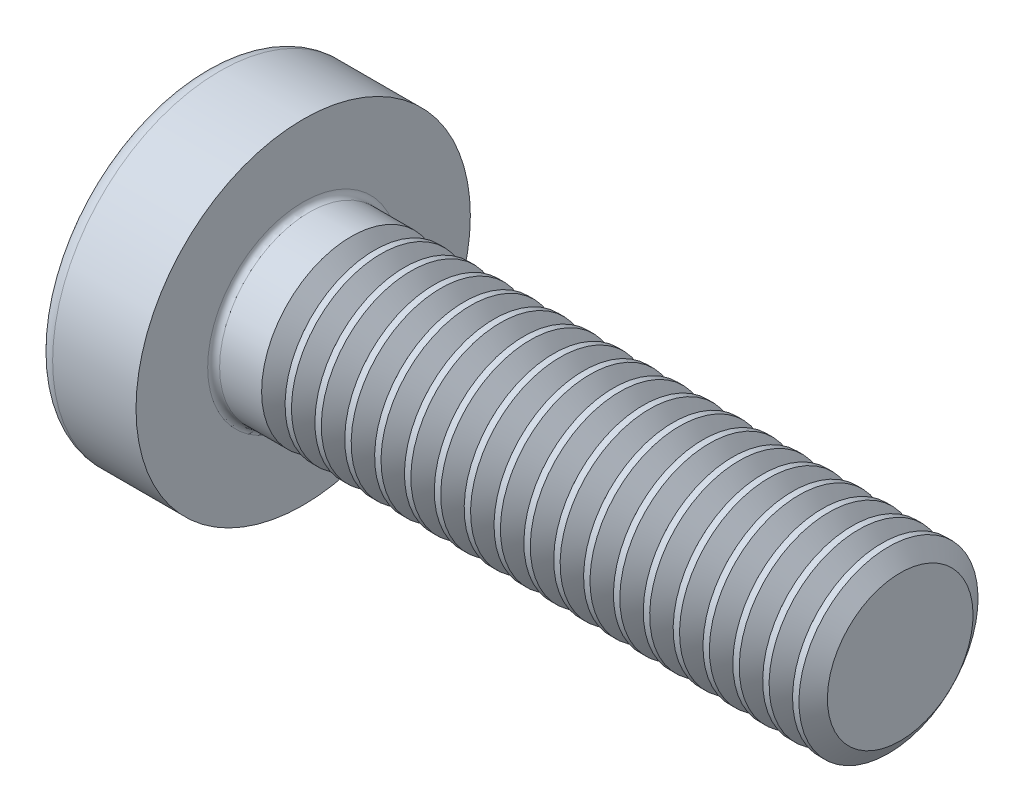
SolidWorks part; units mm, degrees
ref_plane "Plane1" through (0, 0, 0) normal (0, 0, 1) x (1, 0, 0)
ref_plane "Plane2" through (0, 0, 0) normal (0, 1, 0) x (1, 0, 0)
ref_plane "Plane3" through (0, 0, 0) normal (1, 0, 0) x (0, 0, -1)
sketch "BodySke" plane through (0, 0, 0) normal (0, 0, 1) x (1, 0, 0)
  line L0 (2.4, 1.5) -> (2.4, 2.8)
  line L1 (2.65, 6.35) -> (2.65, -3.175) construction
  line L2 (-25.4, 0) -> (127, 0) construction
  line L3 (12.4, 0) -> (0, 0)
  line L4 (2.4, 1.5) -> (12.4, 1.5)
  line L5 (12.4, 1.5) -> (12.4, 0)
  line L6 (1.0035, 2.8) -> (2.4, 2.8)
  line L8 (2.4, 6.35) -> (2.4, -3.175) construction
  arc A0 (0.7754, 2.6744) -> (0, 0) centre (5, 0) ccw
  arc A2 (0.7754, 2.6744) -> (1.0035, 2.8) centre (1.0035, 2.53) cw
  dimension "Head_fillet_rad" = 0.27
  dimension "Head_crown_rad" = 5
  dimension "Head_ht" = 2.4
  dimension "Diameter" = 3
  dimension "Length" = 10
  dimension "Head_dia" = 5.6
  dimension "Advance" = 0.5
  dimension "Thread_nom" = 10
revolve "Base-Revolve" add sketch "BodySke"
cosmetic thread "ThreadCosmetic" [suppressed]
fillet "Fillet1" radius 0.1 1 edges at (2.4, 0, 1.5)
sketch "Sketch3" plane through (0, 0, 0) normal (1, 0, 0) x (0, 0, -1)
  line L0 (0.37, -1.4) -> (-0.37, -1.4)
  line L1 (0.37, -1.4) -> (0.37, 1.4)
  line L2 (-0.37, 1.4) -> (0.37, 1.4)
  line L3 (-0.37, 1.4) -> (-0.37, -1.4)
  dimension "D1" = 1.4
  dimension "Cross_dia" = 2.8
  dimension "D2" = 0.37
  dimension "Cross_width" = 0.74
ref_plane "Plane4" through (1.75, 0, 0) normal (1, 0, 0) x (0, 0, -1)
sketch "Sketch4" plane through (1.75, 0, 0) normal (1, 0, 0) x (0, 0, -1)
  line L0 (0.37, -0.5275) -> (-0.37, -0.5275)
  line L1 (0.37, -0.5275) -> (0.37, 0.5275)
  line L2 (-0.37, 0.5275) -> (0.37, 0.5275)
  line L3 (-0.37, 0.5275) -> (-0.37, -0.5275)
  dimension "D1" = 0.74
  dimension "D2" = 1.055
  dimension "D3" = 0.37
  dimension "D4" = 0.5275
loft "Recess" cut profiles "Sketch3", "Sketch4"
pattern_circular "RecPat" count 2 every 90 about axis through (0, 0, 0) along (1, 0, 0) of "Recess"
sketch "RecCorSke" plane through (0, 0, 0) normal (0, 0, 1) x (1, 0, 0)
  line L0 (-3.175, 0) -> (15.875, 0) construction
  line L1 (-25.4, 0) -> (127, 0) construction
  line L2 (0, 0) -> (0, 0.6784)
  line L3 (0, 0.6784) -> (1.75, 0.556)
  line L4 (1.75, 0.556) -> (1.9307, 0)
  line L5 (1.9307, 0) -> (0, 0)
  dimension "Diameter" = 1.112
  dimension "Depth" = 1.75
  dimension "Draft_angle" = 4
  dimension "Bottom_angle" = 18
revolve "RecessCore" cut sketch "RecCorSke" angle 360 about L0
sketch "ThdSchSke" plane through (0, 0, 0) normal (0, 0, 1) x (1, 0, 0)
  line L0 (3.4, -1.2195) -> (3.2036, -1.5)
  line L1 (3.4, -1.2195) -> (3.5964, -1.5)
  line L2 (3.5964, -1.5) -> (3.5964, -1.875)
  line L3 (-3.175, 0) -> (5.1513, 0) construction
  line L5 (3.5964, -1.875) -> (3.2036, -1.875)
  line L6 (3.2036, -1.875) -> (3.2036, -1.5)
  dimension "Thread_minor" = 2.439
  dimension "Diameter" = 3
  dimension "Start" = 3.4
  dimension "SideAngle" = 55
  dimension "VeeAngle" = 70
  dimension "Overcut" = 3.75
revolve "ThreadSchematic" cut sketch "ThdSchSke" angle 360 about L3
pattern_linear "ThdSchPat" count 19 spacing 0.5 along (1, 0, 0) of "ThreadSchematic"
equation "\"D1@Sketch3\" = \"Cross_dia@Sketch3\" / 2"
equation "\"D2@Sketch3\" = \"Cross_width@Sketch3\" / 2"
equation "\"Depth@RecCorSke\" = \"Cross_depth@Plane4\""
equation "\"D1@Sketch4\" = \"Cross_width@Sketch3\""
equation "\"D2@Sketch4\" = \"Cross_dia@Sketch3\" - 2.0 * \"Cross_depth@Plane4\" * tan(26.5  * 0.017453292)"
equation "\"D3@Sketch4\" = \"D1@Sketch4\" / 2"
equation "\"D4@Sketch4\" = \"D2@Sketch4\" / 2"
equation "\"Thread_length@ThreadCosmetic\" = ((sgn( (\"Length@BodySke\" - \"Advance@BodySke\" * 2.0 ) - \"Thread_nom@BodySke\" )-1)*( (\"Length@BodySke\" - \"Advance@BodySke\" * 2.0 ) - \"Thread_nom@BodySke\" ))/-2+ \"Thread_nom@BodySke\""
equation "\"Thread_minor@ThdSchSke\" = \"Thread_minor@ThreadCosmetic\""
equation "\"Diameter@ThdSchSke\" = \"Diameter@BodySke\""
equation "\"Overcut@ThdSchSke\" = \"Diameter@BodySke\" * 1.25"
equation "\"Start@ThdSchSke\" = \"Head_ht@BodySke\" + \"Length@BodySke\" - \"Thread_length@ThreadCosmetic\"  '---Non-countersunk---"
equation "\"Num_threads@ThdSchPat\" = int( \"Thread_length@ThreadCosmetic\" / \"Advance@BodySke\" + 0.999 )  + 1"
equation "\"Advance@ThdSchPat\" = \"Thread_length@ThreadCosmetic\" /  (\"Num_threads@ThdSchPat\" - 1) 'relax it"
